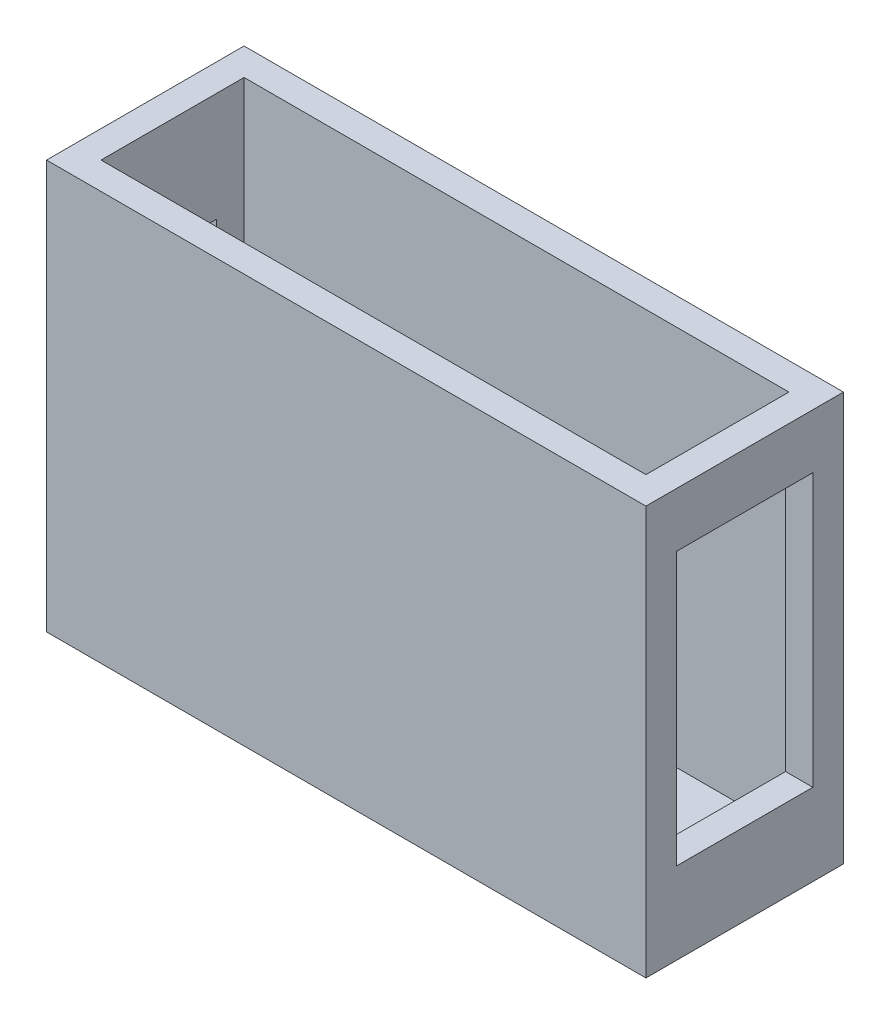
SolidWorks part; units mm, degrees
ref_plane "Front Plane" through (0, 0, 0) normal (0, 0, 1) x (1, 0, 0)
ref_plane "Top Plane" through (0, 0, 0) normal (0, 1, 0) x (1, 0, 0)
ref_plane "Right Plane" through (0, 0, 0) normal (1, 0, 0) x (0, 0, -1)
sketch "Sketch1" plane through (0, 0, 0) normal (0, 1, 0) x (1, 0, 0)
  line L1 (-22, 7.25) -> (22, 7.25)
  line L2 (-22, 7.25) -> (-22, -7.25)
  line L3 (-22, -7.25) -> (22, -7.25)
  line L4 (22, 7.25) -> (22, -7.25)
  line L5 (-22, 7.25) -> (22, -7.25) construction
  line L6 (-22, -7.25) -> (22, 7.25) construction
  line L7 (-20, -5.25) -> (20, -5.25)
  line L8 (-20, -5.25) -> (-20, 5.25)
  line L9 (-20, 5.25) -> (20, 5.25)
  line L10 (20, -5.25) -> (20, 5.25)
  line L11 (-20, -5.25) -> (20, 5.25) construction
  line L12 (-20, 5.25) -> (20, -5.25) construction
  point P0 (0, 0)
  point P6 (0, 0)
  dimension "D1" = 14.5
  dimension "D2" = 44
  dimension "D3" = 40
  dimension "D4" = 10.5
extrude "Boss-Extrude1" add sketch "Sketch1" along normal blind 28
sketch "Sketch2" plane through (0, 0, 0) normal (0, 1, 0) x (1, 0, 0)
  line L1 (-22, -7.25) -> (22, -7.25)
  line L2 (-22, -7.25) -> (-22, 7.25)
  line L3 (-22, 7.25) -> (22, 7.25)
  line L4 (22, -7.25) -> (22, 7.25)
  line L5 (-22, -7.25) -> (22, 7.25) construction
  line L6 (-22, 7.25) -> (22, -7.25) construction
  point P0 (0, 0)
extrude "Boss-Extrude2" add sketch "Sketch2" against normal blind 2
sketch "Sketch3" plane through (-22, 0, 0) normal (-1, 0, 0) x (0, 0, 1)
  line L0 (-5.25, 0) -> (5.25, 0) construction
  line L1 (-3.2343, 8) -> (2.7657, 8)
  line L2 (-3.2343, 8) -> (-3.2343, 20)
  line L3 (-3.2343, 20) -> (2.7657, 20)
  line L4 (2.7657, 8) -> (2.7657, 20)
  line L5 (-3.2343, 8) -> (2.7657, 20) construction
  line L6 (-3.2343, 20) -> (2.7657, 8) construction
  point P0 (-0.2343, 14)
  point P7 (-0.2343, 8)
  dimension "D1" = 14
  dimension "D2" = 12
  dimension "D3" = 6
extrude "Cut-Extrude1" cut sketch "Sketch3" against normal up to next
sketch "Sketch4" plane through (22, 0, 0) normal (1, 0, 0) x (0, 0, -1)
  line L0 (-5.25, 0) -> (5.25, 0) construction
  line L1 (-5, 4) -> (5, 4)
  line L2 (-5, 4) -> (-5, 24)
  line L3 (-5, 24) -> (5, 24)
  line L4 (5, 4) -> (5, 24)
  line L5 (-5, 4) -> (5, 24) construction
  line L6 (-5, 24) -> (5, 4) construction
  point P0 (0, 14)
  dimension "D1" = 14
  dimension "D2" = 20
  dimension "D3" = 10
extrude "Cut-Extrude2" cut sketch "Sketch4" against normal up to next
